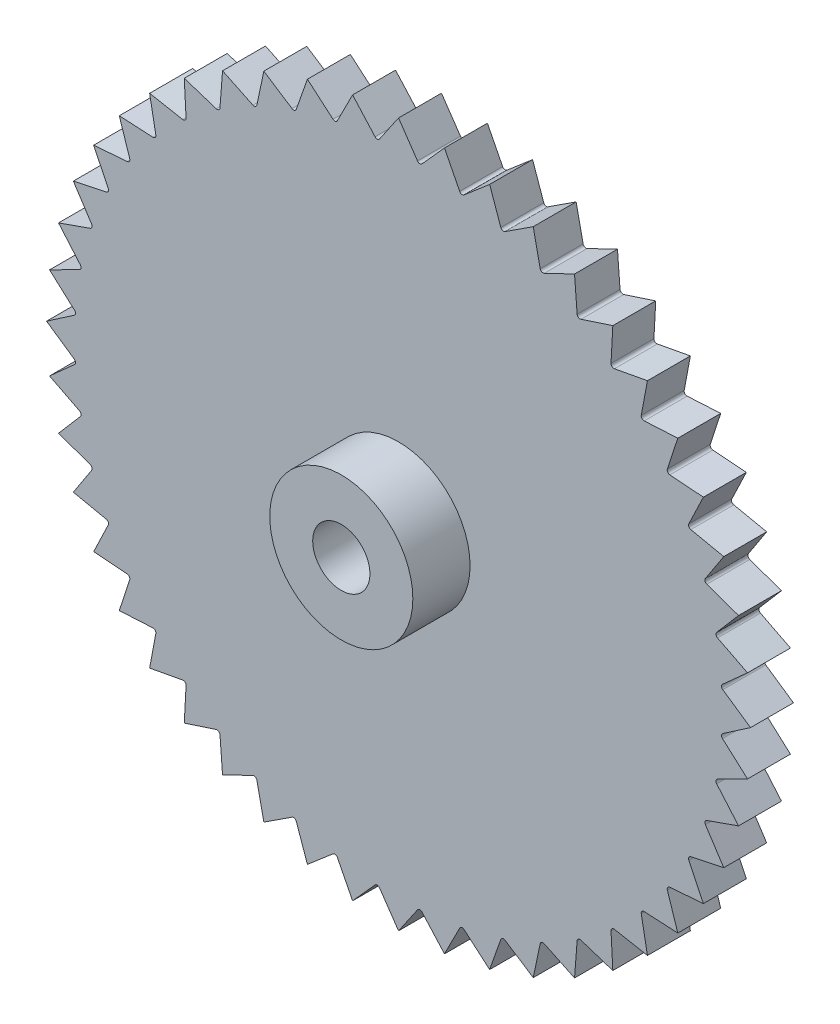
SolidWorks part; units mm, degrees
ref_plane "Front Plane" through (0, 0, 0) normal (0, 0, 1) x (1, 0, 0)
ref_plane "Top Plane" through (0, 0, 0) normal (0, 1, 0) x (1, 0, 0)
ref_plane "Right Plane" through (0, 0, 0) normal (1, 0, 0) x (0, 0, -1)
sketch "Sketch1" plane through (0, 0, 0) normal (0, 0, 1) x (1, 0, 0)
  circle A0 centre (0, 0) radius 12.3
  circle A1 centre (0, 0) radius 1
  dimension "D1" = 24.6
  dimension "D2" = 2
extrude "Boss-Extrude1" add sketch "Sketch1" along normal blind 1.5
sketch "Sketch2" plane through (0, 0, 1.5) normal (0, 0, 1) x (1, 0, 0)
  circle A0 centre (0, 0) radius 1
  circle A1 centre (0, 0) radius 2.5
  dimension "D1" = 5
extrude "Boss-Extrude3" add sketch "Sketch2" along normal blind 2
sketch "Sketch3" plane through (0, 0, 0) normal (0, 0, -1) x (-1, 0, 0)
  circle A0 centre (0, 0) radius 1
  circle A1 centre (0, 0) radius 2.5
extrude "Boss-Extrude4" add sketch "Sketch3" along normal blind 0.5
sketch "Sketch4" plane through (0, 0, 1.5) normal (0, 0, 1) x (1, 0, 0)
  line L0 (1.6055, 12.1948) -> (2.1372, 11.1473)
  line L1 (2.2914, 11.1166) -> (3.1835, 11.8809)
  line L2 (0, 12.3) -> (0.6639, 11.3309)
  line L3 (0.8208, 11.3206) -> (1.6055, 12.1948)
  line L4 (3.1835, 11.8809) -> (3.5739, 10.773)
  line L5 (3.7228, 10.7224) -> (4.707, 11.3637)
  line L6 (4.707, 11.3637) -> (4.9495, 10.2143)
  line L7 (5.0905, 10.1448) -> (6.15, 10.6521)
  line L8 (6.15, 10.6521) -> (6.2404, 9.4809)
  line L9 (6.3711, 9.3935) -> (7.4878, 9.7582)
  line L10 (7.4878, 9.7582) -> (7.4245, 8.5853)
  line L11 (7.5427, 8.4816) -> (8.6974, 8.6974)
  line L12 (8.6974, 8.6974) -> (8.4816, 7.5427)
  line L13 (8.5853, 7.4245) -> (9.7582, 7.4878)
  line L14 (9.7582, 7.4878) -> (9.3935, 6.3711)
  line L15 (9.4809, 6.2404) -> (10.6521, 6.15)
  line L16 (10.6521, 6.15) -> (10.1448, 5.0905)
  line L17 (10.2143, 4.9495) -> (11.3637, 4.707)
  line L18 (11.3637, 4.707) -> (10.7224, 3.7228)
  line L19 (10.773, 3.5739) -> (11.8809, 3.1835)
  line L20 (11.8809, 3.1835) -> (11.1166, 2.2914)
  line L21 (11.1473, 2.1372) -> (12.1948, 1.6055)
  line L22 (12.1948, 1.6055) -> (11.3206, 0.8208)
  line L23 (11.3309, 0.6639) -> (12.3, 0)
  line L24 (12.3, 0) -> (11.3309, -0.6639)
  line L25 (11.3206, -0.8208) -> (12.1948, -1.6055)
  line L26 (12.1948, -1.6055) -> (11.1473, -2.1372)
  line L27 (11.1166, -2.2914) -> (11.8809, -3.1835)
  line L28 (11.8809, -3.1835) -> (10.773, -3.5739)
  line L29 (10.7224, -3.7228) -> (11.3637, -4.707)
  line L30 (11.3637, -4.707) -> (10.2143, -4.9495)
  line L31 (10.1448, -5.0905) -> (10.6521, -6.15)
  line L32 (10.6521, -6.15) -> (9.4809, -6.2404)
  line L33 (9.3935, -6.3711) -> (9.7582, -7.4878)
  line L34 (9.7582, -7.4878) -> (8.5853, -7.4245)
  line L35 (8.4816, -7.5427) -> (8.6974, -8.6974)
  line L36 (8.6974, -8.6974) -> (7.5427, -8.4816)
  line L37 (7.4245, -8.5853) -> (7.4878, -9.7582)
  line L38 (7.4878, -9.7582) -> (6.3711, -9.3935)
  line L39 (6.2404, -9.4809) -> (6.15, -10.6521)
  line L40 (6.15, -10.6521) -> (5.0905, -10.1448)
  line L41 (4.9495, -10.2143) -> (4.707, -11.3637)
  line L42 (4.707, -11.3637) -> (3.7228, -10.7224)
  line L43 (3.5739, -10.773) -> (3.1835, -11.8809)
  line L44 (3.1835, -11.8809) -> (2.2914, -11.1166)
  line L45 (2.1372, -11.1473) -> (1.6055, -12.1948)
  line L46 (1.6055, -12.1948) -> (0.8208, -11.3206)
  line L47 (0.6639, -11.3309) -> (0, -12.3)
  line L48 (0, -12.3) -> (-0.6639, -11.3309)
  line L49 (-0.8208, -11.3206) -> (-1.6055, -12.1948)
  line L50 (-1.6055, -12.1948) -> (-2.1372, -11.1473)
  line L51 (-2.2914, -11.1166) -> (-3.1835, -11.8809)
  line L52 (-3.1835, -11.8809) -> (-3.5739, -10.773)
  line L53 (-3.7228, -10.7224) -> (-4.707, -11.3637)
  line L54 (-4.707, -11.3637) -> (-4.9495, -10.2143)
  line L55 (-5.0905, -10.1448) -> (-6.15, -10.6521)
  line L56 (-6.15, -10.6521) -> (-6.2404, -9.4809)
  line L57 (-6.3711, -9.3935) -> (-7.4878, -9.7582)
  line L58 (-7.4878, -9.7582) -> (-7.4245, -8.5853)
  line L59 (-7.5427, -8.4816) -> (-8.6974, -8.6974)
  line L60 (-8.6974, -8.6974) -> (-8.4816, -7.5427)
  line L61 (-8.5853, -7.4245) -> (-9.7582, -7.4878)
  line L62 (-9.7582, -7.4878) -> (-9.3935, -6.3711)
  line L63 (-9.4809, -6.2404) -> (-10.6521, -6.15)
  line L64 (-10.6521, -6.15) -> (-10.1448, -5.0905)
  line L65 (-10.2143, -4.9495) -> (-11.3637, -4.707)
  line L66 (-11.3637, -4.707) -> (-10.7224, -3.7228)
  line L67 (-10.773, -3.5739) -> (-11.8809, -3.1835)
  line L68 (-11.8809, -3.1835) -> (-11.1166, -2.2914)
  line L69 (-11.1473, -2.1372) -> (-12.1948, -1.6055)
  line L70 (-12.1948, -1.6055) -> (-11.3206, -0.8208)
  line L71 (-11.3309, -0.6639) -> (-12.3, 0)
  line L72 (-12.3, 0) -> (-11.3309, 0.6639)
  line L73 (-11.3206, 0.8208) -> (-12.1948, 1.6055)
  line L74 (-12.1948, 1.6055) -> (-11.1473, 2.1372)
  line L75 (-11.1166, 2.2914) -> (-11.8809, 3.1835)
  line L76 (-11.8809, 3.1835) -> (-10.773, 3.5739)
  line L77 (-10.7224, 3.7228) -> (-11.3637, 4.707)
  line L78 (-11.3637, 4.707) -> (-10.2143, 4.9495)
  line L79 (-10.1448, 5.0905) -> (-10.6521, 6.15)
  line L80 (-10.6521, 6.15) -> (-9.4809, 6.2404)
  line L81 (-9.3935, 6.3711) -> (-9.7582, 7.4878)
  line L82 (-9.7582, 7.4878) -> (-8.5853, 7.4245)
  line L83 (-8.4816, 7.5427) -> (-8.6974, 8.6974)
  line L84 (-8.6974, 8.6974) -> (-7.5427, 8.4816)
  line L85 (-7.4245, 8.5853) -> (-7.4878, 9.7582)
  line L86 (-7.4878, 9.7582) -> (-6.3711, 9.3935)
  line L87 (-6.2404, 9.4809) -> (-6.15, 10.6521)
  line L88 (-6.15, 10.6521) -> (-5.0905, 10.1448)
  line L89 (-4.9495, 10.2143) -> (-4.707, 11.3637)
  line L90 (-4.707, 11.3637) -> (-3.7228, 10.7224)
  line L91 (-3.5739, 10.773) -> (-3.1835, 11.8809)
  line L92 (-3.1835, 11.8809) -> (-2.2914, 11.1166)
  line L93 (-2.1372, 11.1473) -> (-1.6055, 12.1948)
  line L94 (-1.6055, 12.1948) -> (-0.8208, 11.3206)
  line L95 (-0.6639, 11.3309) -> (0, 12.3)
  circle A0 centre (0, 0) radius 12.3 construction
  arc A2 (0.6639, 11.3309) -> (0.8208, 11.3206) centre (0.7464, 11.3874) ccw
  arc A3 (2.1372, 11.1473) -> (2.2914, 11.1166) centre (2.2263, 11.1926) ccw
  arc A4 (3.5739, 10.773) -> (3.7228, 10.7224) centre (3.6682, 10.8062) ccw
  arc A5 (4.9495, 10.2143) -> (5.0905, 10.1448) centre (5.0473, 10.235) ccw
  arc A6 (6.2404, 9.4809) -> (6.3711, 9.3935) centre (6.3401, 9.4886) ccw
  arc A7 (7.4245, 8.5853) -> (7.5427, 8.4816) centre (7.5243, 8.5799) ccw
  arc A8 (8.4816, 7.5427) -> (8.5853, 7.4245) centre (8.5799, 7.5243) ccw
  arc A9 (9.3935, 6.3711) -> (9.4809, 6.2404) centre (9.4886, 6.3401) ccw
  arc A10 (10.1448, 5.0905) -> (10.2143, 4.9495) centre (10.235, 5.0473) ccw
  arc A11 (10.7224, 3.7228) -> (10.773, 3.5739) centre (10.8062, 3.6682) ccw
  arc A12 (11.1166, 2.2914) -> (11.1473, 2.1372) centre (11.1926, 2.2263) ccw
  arc A13 (11.3206, 0.8208) -> (11.3309, 0.6639) centre (11.3874, 0.7464) ccw
  arc A14 (11.3309, -0.6639) -> (11.3206, -0.8208) centre (11.3874, -0.7464) ccw
  arc A15 (11.1473, -2.1372) -> (11.1166, -2.2914) centre (11.1926, -2.2263) ccw
  arc A16 (10.773, -3.5739) -> (10.7224, -3.7228) centre (10.8062, -3.6682) ccw
  arc A17 (10.2143, -4.9495) -> (10.1448, -5.0905) centre (10.235, -5.0473) ccw
  arc A18 (9.4809, -6.2404) -> (9.3935, -6.3711) centre (9.4886, -6.3401) ccw
  arc A19 (8.5853, -7.4245) -> (8.4816, -7.5427) centre (8.5799, -7.5243) ccw
  arc A20 (7.5427, -8.4816) -> (7.4245, -8.5853) centre (7.5243, -8.5799) ccw
  arc A21 (6.3711, -9.3935) -> (6.2404, -9.4809) centre (6.3401, -9.4886) ccw
  arc A22 (5.0905, -10.1448) -> (4.9495, -10.2143) centre (5.0473, -10.235) ccw
  arc A23 (3.7228, -10.7224) -> (3.5739, -10.773) centre (3.6682, -10.8062) ccw
  arc A24 (2.2914, -11.1166) -> (2.1372, -11.1473) centre (2.2263, -11.1926) ccw
  arc A25 (0.8208, -11.3206) -> (0.6639, -11.3309) centre (0.7464, -11.3874) ccw
  arc A26 (-0.6639, -11.3309) -> (-0.8208, -11.3206) centre (-0.7464, -11.3874) ccw
  arc A27 (-2.1372, -11.1473) -> (-2.2914, -11.1166) centre (-2.2263, -11.1926) ccw
  arc A28 (-3.5739, -10.773) -> (-3.7228, -10.7224) centre (-3.6682, -10.8062) ccw
  arc A29 (-4.9495, -10.2143) -> (-5.0905, -10.1448) centre (-5.0473, -10.235) ccw
  arc A30 (-6.2404, -9.4809) -> (-6.3711, -9.3935) centre (-6.3401, -9.4886) ccw
  arc A31 (-7.4245, -8.5853) -> (-7.5427, -8.4816) centre (-7.5243, -8.5799) ccw
  arc A32 (-8.4816, -7.5427) -> (-8.5853, -7.4245) centre (-8.5799, -7.5243) ccw
  arc A33 (-9.3935, -6.3711) -> (-9.4809, -6.2404) centre (-9.4886, -6.3401) ccw
  arc A34 (-10.1448, -5.0905) -> (-10.2143, -4.9495) centre (-10.235, -5.0473) ccw
  arc A35 (-10.7224, -3.7228) -> (-10.773, -3.5739) centre (-10.8062, -3.6682) ccw
  arc A36 (-11.1166, -2.2914) -> (-11.1473, -2.1372) centre (-11.1926, -2.2263) ccw
  arc A37 (-11.3206, -0.8208) -> (-11.3309, -0.6639) centre (-11.3874, -0.7464) ccw
  arc A38 (-11.3309, 0.6639) -> (-11.3206, 0.8208) centre (-11.3874, 0.7464) ccw
  arc A39 (-11.1473, 2.1372) -> (-11.1166, 2.2914) centre (-11.1926, 2.2263) ccw
  arc A40 (-10.773, 3.5739) -> (-10.7224, 3.7228) centre (-10.8062, 3.6682) ccw
  arc A41 (-10.2143, 4.9495) -> (-10.1448, 5.0905) centre (-10.235, 5.0473) ccw
  arc A42 (-9.4809, 6.2404) -> (-9.3935, 6.3711) centre (-9.4886, 6.3401) ccw
  arc A43 (-8.5853, 7.4245) -> (-8.4816, 7.5427) centre (-8.5799, 7.5243) ccw
  arc A44 (-7.5427, 8.4816) -> (-7.4245, 8.5853) centre (-7.5243, 8.5799) ccw
  arc A45 (-6.3711, 9.3935) -> (-6.2404, 9.4809) centre (-6.3401, 9.4886) ccw
  arc A46 (-5.0905, 10.1448) -> (-4.9495, 10.2143) centre (-5.0473, 10.235) ccw
  arc A47 (-3.7228, 10.7224) -> (-3.5739, 10.773) centre (-3.6682, 10.8062) ccw
  arc A48 (-2.2914, 11.1166) -> (-2.1372, 11.1473) centre (-2.2263, 11.1926) ccw
  arc A49 (-0.8208, 11.3206) -> (-0.6639, 11.3309) centre (-0.7464, 11.3874) ccw
  circle A50 centre (0, 0) radius 15.2947
  point P17 (0, 0)
  point P23 (0, 0)
  point P29 (0, 0)
  point P35 (0, 0)
  point P41 (0, 0)
  point P47 (0, 0)
  point P53 (0, 0)
  point P55 (0, 0)
  point P60 (0, 0)
  point P66 (0, 0)
  point P72 (0, 0)
  point P78 (0, 0)
  point P84 (0, 0)
  point P90 (0, 0)
  point P96 (0, 0)
  point P102 (0, 0)
  point P108 (0, 0)
  point P114 (0, 0)
  point P120 (0, 0)
  point P126 (0, 0)
  point P132 (0, 0)
  point P138 (0, 0)
  point P144 (0, 0)
  point P150 (0, 0)
  point P156 (0, 0)
  point P162 (0, 0)
  point P168 (0, 0)
  point P174 (0, 0)
  point P180 (0, 0)
  point P186 (0, 0)
  point P192 (0, 0)
  point P198 (0, 0)
  point P204 (0, 0)
  point P210 (0, 0)
  point P216 (0, 0)
  point P222 (0, 0)
  point P228 (0, 0)
  point P234 (0, 0)
  point P240 (0, 0)
  point P246 (0, 0)
  point P252 (0, 0)
  point P258 (0, 0)
  point P264 (0, 0)
  point P270 (0, 0)
  point P276 (0, 0)
  point P282 (0, 0)
  point P288 (0, 0)
  point P294 (0, 0)
  point P295 (0, 0)
  dimension "D2" = 48
  dimension "D1" = 0.1
extrude "Cut-Extrude1" cut sketch "Sketch4" against normal through all
